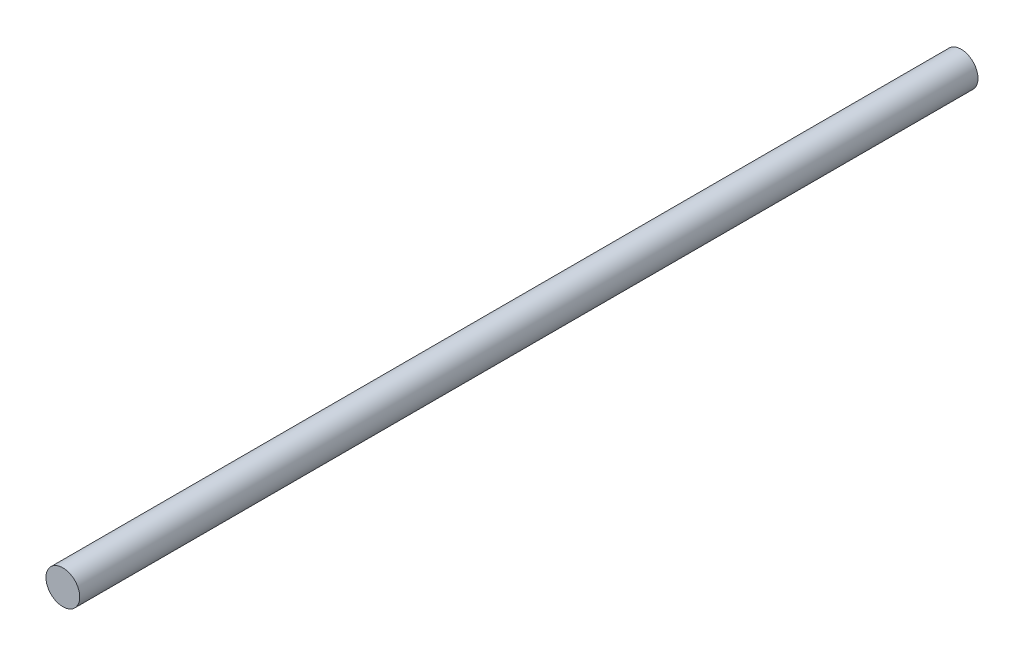
SolidWorks part; units mm, degrees
material "AISI 1020"
ref_plane "Front Plane" through (0, 0, 0) normal (0, 0, 1) x (1, 0, 0)
ref_plane "Top Plane" through (0, 0, 0) normal (0, 1, 0) x (1, 0, 0)
ref_plane "Right Plane" through (0, 0, 0) normal (1, 0, 0) x (0, 0, -1)
sketch "Sketch1" plane through (0, 0, 0) normal (0, 0, 1) x (1, 0, 0)
  circle A0 centre (-8.7611, 6.9241) radius 5
  dimension "D1" = 10
extrude "Boss-Extrude1" add sketch "Sketch1" along normal blind 266
